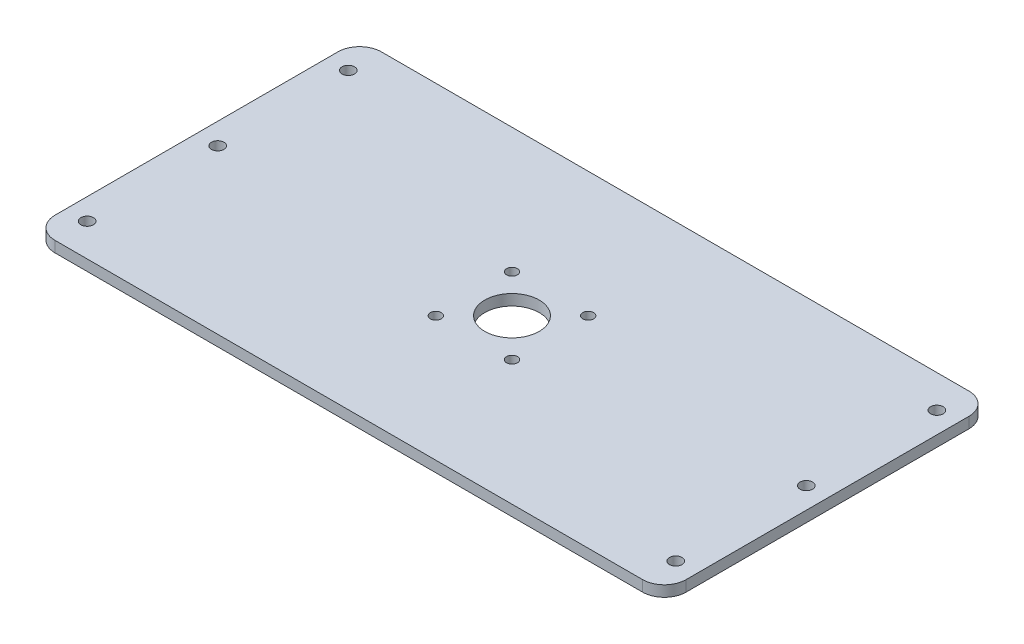
SolidWorks part; units mm, degrees
ref_plane "Front Plane" through (0, 0, 0) normal (0, 0, 1) x (1, 0, 0)
ref_plane "Top Plane" through (0, 0, 0) normal (0, 1, 0) x (1, 0, 0)
ref_plane "Right Plane" through (0, 0, 0) normal (1, 0, 0) x (0, 0, -1)
sketch "Sketch1" plane through (0, 0, 0) normal (0, 1, 0) x (1, 0, 0)
  line L1 (145, -75) -> (-145, -75)
  line L2 (145, -75) -> (145, 75)
  line L3 (145, 75) -> (-145, 75)
  line L4 (-145, -75) -> (-145, 75)
  line L14 (-145, 0) -> (-138.1, 0) construction
  line L15 (-132.35, 0) -> (-132.35, 1.2253)
  circle A0 centre (-135.225, 0) radius 2.875
  circle A1 centre (135.225, 0) radius 2.875
  circle A2 centre (135.225, 60) radius 2.875
  circle A3 centre (-135.225, 60) radius 2.875
  circle A4 centre (-135.225, -60) radius 2.875
  circle A5 centre (135.225, -60) radius 2.875
  circle A6 centre (0, 0) radius 12.5
  circle A7 centre (-17.5, 17.5) radius 2.5
  circle A8 centre (17.5, 17.5) radius 2.5
  circle A9 centre (17.5, -17.5) radius 2.5
  circle A10 centre (-17.5, -17.5) radius 2.5
  point P0 (0, 0)
  dimension "D7" = 60
  dimension "D8" = 270.45
  dimension "D9" = 2
  dimension "D1" = 290
  dimension "D2" = 150
  dimension "D5" = 2
  dimension "D6" = 2
  dimension "D10" = 2
extrude "Boss-Extrude2" add sketch "Sketch1" along normal blind 5
fillet "Fillet1" radius 10 4 edges at (-145, 2.5, -75) (145, 2.5, -75) (145, 2.5, 75) (-145, 2.5, 75)
